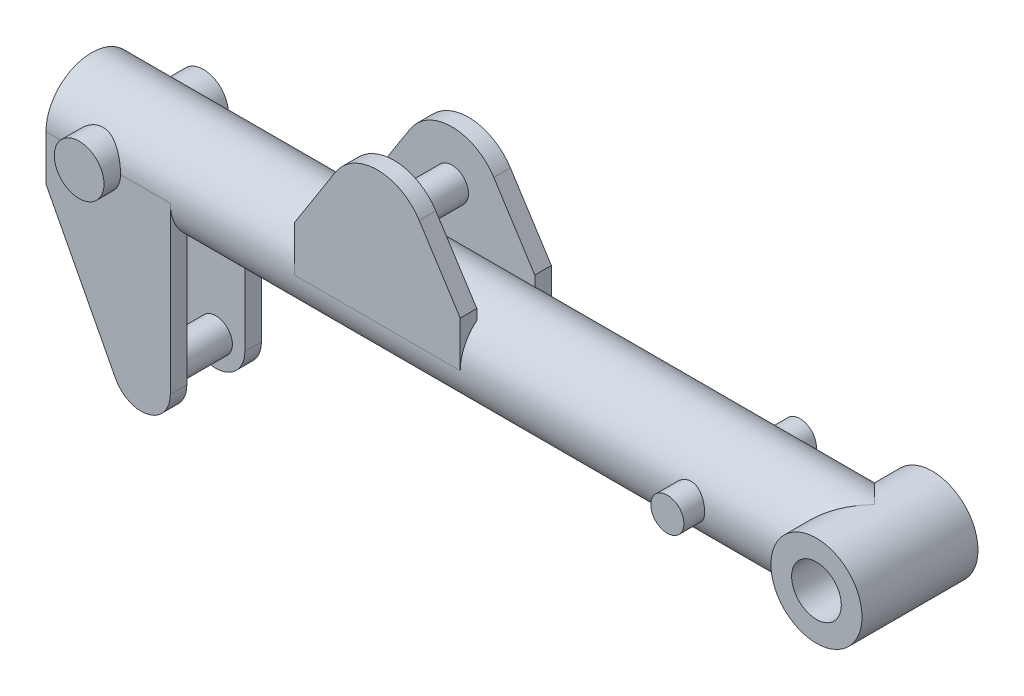
SolidWorks part; units mm, degrees
material "AISI 4340 Steel, normalized"
ref_plane "Front Plane" through (0, 0, 0) normal (0, 0, 1) x (1, 0, 0)
ref_plane "Top Plane" through (0, 0, 0) normal (0, 1, 0) x (1, 0, 0)
ref_plane "Right Plane" through (0, 0, 0) normal (1, 0, 0) x (0, 0, -1)
sketch "Sketch1" plane through (0, 0, 0) normal (1, 0, 0) x (0, 0, -1)
  circle A0 centre (0, 0) radius 55
  dimension "D1" = 110
extrude "Boss-Extrude1" add sketch "Sketch1" along normal blind 1000
shell "Shell1" thickness 10
sketch "Sketch2" plane through (0, 0, 0) normal (0, 0, 1) x (1, 0, 0)
  circle A0 centre (60, 0) radius 30
  dimension "D1" = 60
  dimension "D2" = 60
ref_plane "Plane1" through (0, 0, 55) normal (0, 0, 1) x (1, 0, 0)
sketch "Sketch3" plane through (0, 0, 55) normal (0, 0, 1) x (1, 0, 0)
  line L0 (300, 0) -> (300, 55)
  line L1 (500, 55) -> (450.5469, 132.3266)
  line L3 (300, 0) -> (500, 0)
  line L4 (500, 0) -> (500, 55)
  line L6 (1000, -55) -> (1000, 55) construction
  line L7 (300, 55) -> (349.4531, 132.3266)
  line L8 (1000, 55) -> (0, 55) construction
  line L9 (150, 0) -> (150, -55)
  line L10 (0, -55) -> (1000, -55) construction
  line L11 (150, -55) -> (150, -200)
  line L12 (0, 0) -> (0, -55)
  line L13 (0, -55) -> (83.9593, -216.1702)
  line L14 (0, 0) -> (150, 0)
  line L15 (0, 55) -> (0, -55) construction
  arc A0 (450.5469, 132.3266) -> (349.4531, 132.3266) centre (400, 100) ccw
  circle A1 centre (400, 100) radius 20 construction
  arc A2 (83.9593, -216.1702) -> (150, -200) centre (115, -200) ccw
  circle A3 centre (115, -200) radius 20 construction
  point P14 (400, 0)
  point P23 (183.4898, -134.6514)
  dimension "D1" = 40
  dimension "D2" = 40
  dimension "D6" = 150
  dimension "D8" = 40
  dimension "D9" = 15
  dimension "D3" = 100
  dimension "D4" = 500
  dimension "D5" = 200
  dimension "D7" = 200
extrude "Boss-Extrude2" add sketch "Sketch3" against normal blind 20 separate body
sketch "Sketch4" plane through (1000, 0, 0) normal (1, 0, 0) x (0, 0, -1)
  line L0 (0, 55) -> (0, -55) construction
  circle A0 centre (0, 0) radius 55 construction
ref_plane "Plane2" through (0, 0, 0) normal (0, 0, 1) x (1, 0, 0)
mirror "Mirror2" about plane through (0, 0, 0) normal (0, 0, 1) of "Boss-Extrude2"
sketch "Sketch5" plane through (0, 0, 0) normal (0, 0, 1) x (1, 0, 0)
  line L0 (60.5, 0) -> (-60.5, 0) construction
  line L1 (1000, 55) -> (0, 55) construction
  line L2 (1000, -55) -> (1000, 55) construction
  circle A0 centre (945, 0) radius 55
extrude "Boss-Extrude3" add sketch "Sketch5" along normal mid plane 140
sketch "Sketch6" plane through (0, 0, 70) normal (0, 0, 1) x (1, 0, 0)
  line L0 (1000, 55) -> (1000, -55)
  line L1 (1000, -55) -> (1000, 0) construction
  line L2 (1000, -55) -> (945, -55)
  line L3 (1000, 55) -> (945, 55)
  circle A0 centre (945, 0) radius 30
  arc A1 (945, -55) -> (945, 55) centre (945, 0) ccw
  arc A2 (945, 55) -> (945, -55) centre (945, 0) ccw construction
  circle M3 centre (945, 0) radius 55
  dimension "D1" = 60
extrude "Cut-Extrude2" cut sketch "Sketch6" against normal through all contours A0 | L0 L3 M3 | L2 L0 M3
extrude "Boss-Extrude4" add sketch "Sketch2" along normal mid plane 150
sketch "Sketch7" plane through (0, 0, 0) normal (0, 0, 1) x (1, 0, 0)
  circle A1 centre (400, 100) radius 20 construction
  circle A2 centre (400, 100) radius 20
  circle A3 centre (115, -200) radius 20 construction
  circle A4 centre (115, -200) radius 20
extrude "Boss-Extrude5" add sketch "Sketch7" along normal mid plane 110
sketch "Sketch8" plane through (0, 0, 0) normal (0, 0, 1) x (1, 0, 0)
  circle A0 centre (775, 0) radius 20
  point P2 (945, 0)
  dimension "D1" = 40
  dimension "D2" = 170
extrude "Boss-Extrude6" add sketch "Sketch8" along normal mid plane 160
